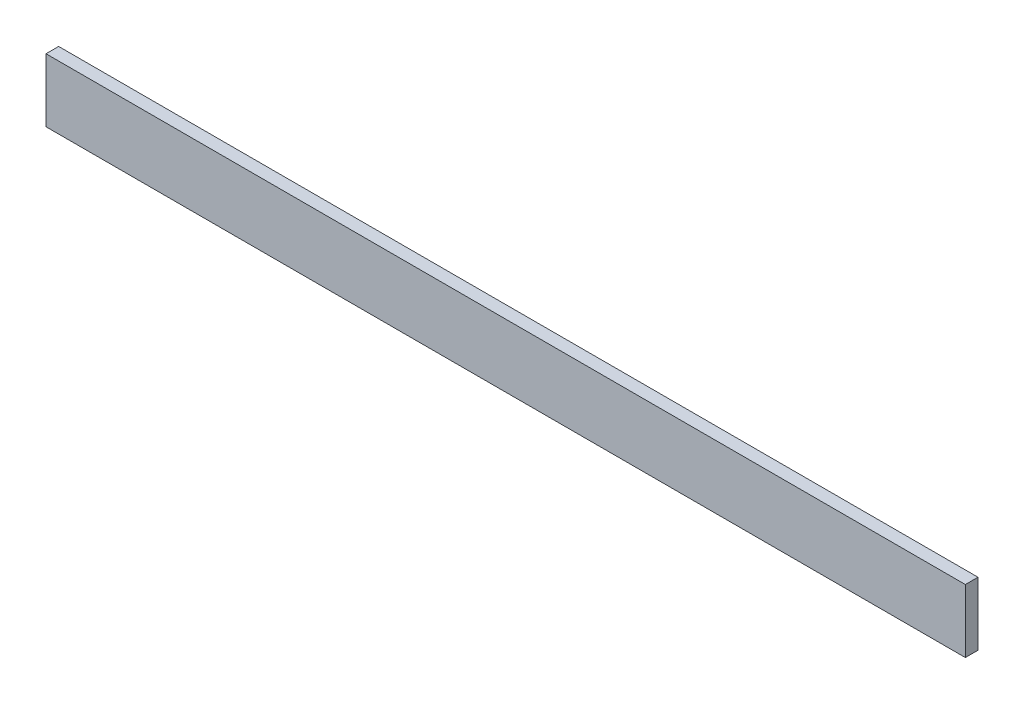
SolidWorks part; units mm, degrees
ref_plane "Front Plane" through (0, 0, 0) normal (0, 0, 1) x (1, 0, 0)
ref_plane "Top Plane" through (0, 0, 0) normal (0, 1, 0) x (1, 0, 0)
ref_plane "Right Plane" through (0, 0, 0) normal (1, 0, 0) x (0, 0, -1)
sketch "Sketch1" plane through (0, 0, 0) normal (0, 0, 1) x (1, 0, 0)
  line L1 (0, 0) -> (2768.6, 0)
  line L2 (0, 0) -> (0, 190.5)
  line L3 (0, 190.5) -> (2768.6, 190.5)
  line L4 (2768.6, 0) -> (2768.6, 190.5)
  dimension "D1" = 2768.6
  dimension "D2" = 190.5
extrude "Boss-Extrude1" add sketch "Sketch1" along normal blind 38.1
